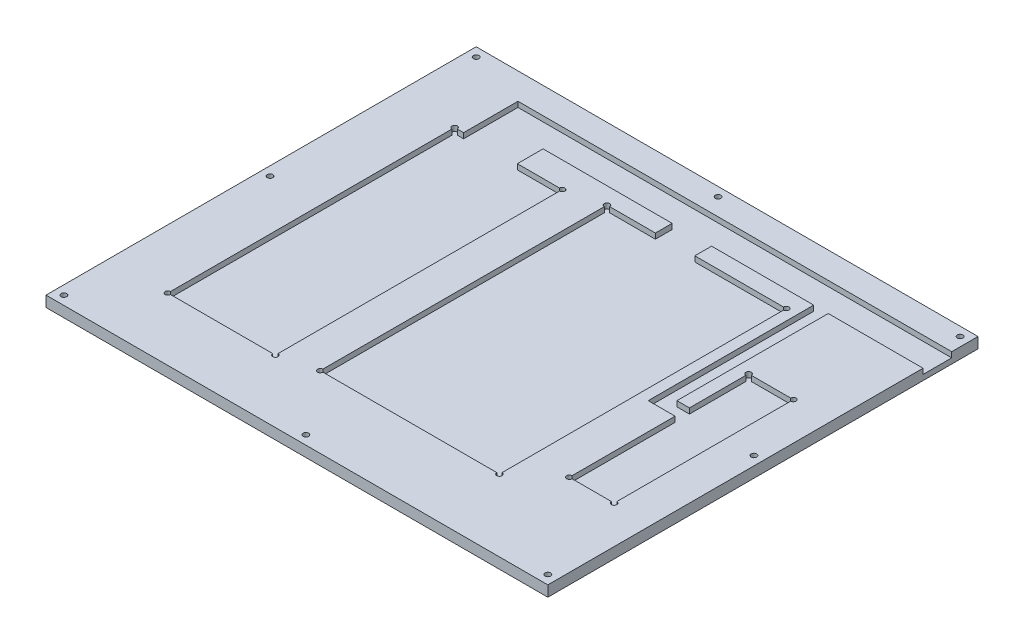
SolidWorks part; units mm, degrees
ref_plane "Спереди" through (0, 0, 0) normal (0, 0, 1) x (1, 0, 0)
ref_plane "Сверху" through (0, 0, 0) normal (0, 1, 0) x (1, 0, 0)
ref_plane "Справа" through (0, 0, 0) normal (1, 0, 0) x (0, 0, -1)
sketch "Эскиз1" plane through (0, 0, 0) normal (0, 1, 0) x (1, 0, 0)
  line L1 (-140, 120) -> (140, 120)
  line L2 (-140, 120) -> (-140, -120)
  line L3 (-140, -120) -> (140, -120)
  line L4 (140, 120) -> (140, -120)
  line L5 (-140, 120) -> (140, -120) construction
  line L6 (-140, -120) -> (140, 120) construction
  point P0 (0, 0)
extrude "Бобышка-Вытянуть1" add sketch "Эскиз1" along normal blind 6
ref_plane "Плоскость1" through (140, 6, 120) normal (1, 0, 0) x (0, 0, -1)
sketch "Эскиз4" plane through (0, 6, 0) normal (0, 1, 0) x (1, 0, 0)
  line L0 (0, 144.5058) -> (0, -142.1688) construction
  line L1 (0, 0) -> (220.0198, 0) construction
  point P0 (135, 115)
  point P6 (0, 115)
  point P7 (135, 0)
  point P8 (0, -115)
  point P9 (135, -115)
  point P10 (-135, -115)
  point P11 (-135, 0)
  point P12 (-135, 115)
hole_wizard "Диаметр отверстия Ø3.1 (3.1)1" positions "Эскиз6" profile "Эскиз5" hole size "Ø3.1" standard "ISO"
sketch "Эскиз6" plane through (0, 6, 0) normal (0, 1, 0) x (1, 0, 0)
  point P0 (-135, 115)
  point P3 (0, 115)
  point P6 (135, 115)
  point P9 (135, 0)
  point P12 (135, -115)
  point P15 (0, -115)
  point P18 (-135, -115)
  point P21 (-135, 0)
  point P24 (401.5232, 110.9951)
sketch "Эскиз5" plane through (-135, 6, -115) normal (1, 0, 0) x (0, 0, 1)
  line L0 (0, 0) -> (0, 10.9313)
  line L1 (0, 10.9313) -> (1.55, 10)
  line L2 (1.55, 10) -> (1.55, 0)
  line L5 (1.55, 0) -> (0, 0)
  line L10 (0, 10.9313) -> (-1.55, 10) construction
  line L11 (0, -6.35) -> (0, 107.95) construction
  dimension "Диаметр отверстия" = 3.1
  dimension "Глубина отверстия" = 10
  dimension "Угол заточки сверла" = 118
sketch "Эскиз7" plane through (0, 6, 0) normal (0, 1, 0) x (1, 0, 0)
  line L1 (119, 38) -> (94, 38)
  line L2 (119, 38) -> (119, -62)
  line L3 (119, -62) -> (94, -62)
  line L4 (94, 38) -> (94, -62)
  line L5 (73, 80) -> (-27, 80)
  line L6 (73, 80) -> (73, -80)
  line L7 (73, -80) -> (-27, -80)
  line L8 (-27, 80) -> (-27, -80)
  line L9 (-47, 75) -> (-107, 75)
  line L10 (-47, 75) -> (-47, -85)
  line L11 (-47, -85) -> (-107, -85)
  line L12 (-107, 75) -> (-107, -85)
  circle A0 centre (119, 38) radius 1.5
  circle A1 centre (119, -62) radius 1.5
  circle A2 centre (94, -62) radius 1.5
  circle A3 centre (94, 38) radius 1.5
  circle A4 centre (73, -80) radius 1.5
  circle A5 centre (73, 80) radius 1.5
  circle A6 centre (-27, -80) radius 1.5
  circle A7 centre (-27, 80) radius 1.5
  circle A8 centre (-47, -85) radius 1.5
  circle A9 centre (-47, 75) radius 1.5
  circle A10 centre (-107, 75) radius 1.5
  circle A11 centre (-107, -85) radius 1.5
extrude "Вырез-Вытянуть1" cut sketch "Эскиз7" against normal blind 3 contours L2 A0 L1 | A3 L4 A2 L3 A1 L2 A0 L1 | L1 A0 L2 | L1 A3 L4 | L4 A3 L1 | L4 A2 L3 | L3 A2 L4 | L3 A1 L2 | L2 A1 L3 | A7 L8 A6 L7 A4 L6 A5 L5 | A11 L11 A8 L10 A9 L9 A10 L12 | L5 A5 L6 | L6 A5 L5 | L7 A4 L6 | L6 A4 L7 | L8 A6 L7 | L7 A6 L8 | L5 A7 L8 | L8 A7 L5 | L9 A9 L10 | L10 A9 L9 | L10 A8 L11 | L11 A8 L10 | L11 A11 L12 | L12 A11 L11 | L9 A10 L12 | L12 A10 L9
sketch "Эскиз8" plane through (0, 6, 0) normal (0, 1, 0) x (1, 0, 0)
  line L0 (94, 36.5) -> (94, -60.5) construction
  line L1 (87.1211, 89.3355) -> (140, 89.3355)
  line L2 (87, 5) -> (94, 5)
  line L3 (94, 36.5) -> (94, -60.5) construction
  line L4 (94, -3) -> (94, 5)
  line L5 (22, 80) -> (22.0247, 89.3355)
  line L6 (87, 5) -> (87.1211, 89.3355)
  line L7 (22, 105.3355) -> (-42.9797, 105.3355)
  line L8 (94, -3) -> (79, -3)
  line L9 (79, -3) -> (79, 89.3355)
  line L10 (0, 80) -> (22, 80)
  line L11 (0, 89.3355) -> (-72, 89.3355)
  line L12 (-72, 75) -> (-72, 89.3355)
  line L13 (71.5, 80) -> (-25.5, 80) construction
  line L14 (0, 144.5058) -> (0, -142.1688) construction
  line L15 (0, 80) -> (0, 89.3355)
  line L16 (79, 89.3355) -> (22.0247, 89.3355)
  line L17 (140, 89.3355) -> (140, 105.3355)
  line L19 (-102, 89.3355) -> (-102, 105.3355)
  line L20 (-102, 75) -> (-102, 89.3355)
  line L21 (-102, 105.3355) -> (-42.9797, 105.3355)
  line L22 (-102, 75) -> (-72, 75)
  line L23 (22, 105.3355) -> (140, 105.3355)
  line L24 (140, -120) -> (140, 120) construction
extrude "Вырез-Вытянуть2" cut sketch "Эскиз8" against normal blind 3
